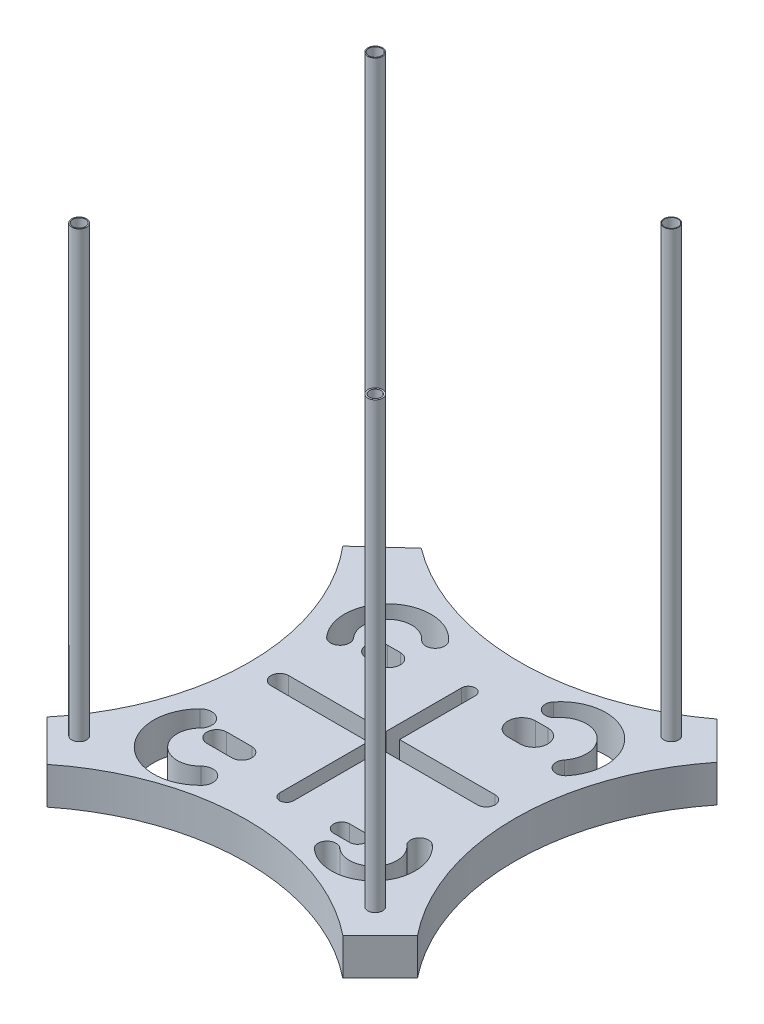
SolidWorks part; units mm, degrees
material "ABS"
ref_plane "Front Plane" through (0, 0, 0) normal (0, 0, 1) x (1, 0, 0)
ref_plane "Top Plane" through (0, 0, 0) normal (0, 1, 0) x (1, 0, 0)
ref_plane "Right Plane" through (0, 0, 0) normal (1, 0, 0) x (0, 0, -1)
sketch "Sketch1" plane through (0, 0, 0) normal (0, 1, 0) x (1, 0, 0)
  line L4 (-35.4489, 52.7329) -> (-27.9489, 60.2329)
  line L5 (12.0511, 60.2329) -> (19.5511, 52.7329)
  line L6 (19.5511, 52.7329) -> (19.6053, 52.733)
  line L7 (19.5511, 12.733) -> (12.0511, 5.2329)
  line L9 (-27.9489, 5.2329) -> (-35.4489, 12.7329)
  arc A4 (19.5511, 52.7329) -> (19.5511, 12.733) centre (42.4677, 32.7329) ccw
  arc A5 (-35.4489, 52.7329) -> (-35.4489, 12.7329) centre (-58.3656, 32.7329) cw
  arc A6 (12.0511, 60.2329) -> (-27.9489, 60.2329) centre (-7.9489, 83.1496) cw
  arc A7 (12.0511, 5.2329) -> (-2.9489, 12.3192) centre (-7.9489, -17.6837) ccw
  arc A8 (-12.9489, 12.3192) -> (-27.9489, 5.2329) centre (-7.9489, -17.6837) ccw
  arc A9 (-12.9489, 12.3192) -> (-2.9489, 12.3192) centre (-7.9489, -11.0454) cw
extrude "Boss-Extrude1" add sketch "Sketch1" along normal blind 5
sketch "Sketch3" plane through (0, 5, 0) normal (0, 1, 0) x (1, 0, 0)
  line L0 (-27.9489, 60.2329) -> (-35.4489, 52.7329)
  line L1 (12.0511, 60.2329) -> (19.5511, 52.7329)
  line L2 (-35.4489, 12.7329) -> (-27.9489, 5.2329)
  line L3 (12.0511, 5.2329) -> (19.5511, 12.733)
  line L4 (-33.4937, 12.7329) -> (-27.9489, 7.1882)
  line L5 (12.0511, 7.1882) -> (17.0997, 12.2368)
  line L8 (-33.4937, 52.7329) -> (-27.9489, 57.7816)
  line L9 (12.0511, 57.7816) -> (17.0997, 52.7329)
  arc A0 (-27.9489, 60.2329) -> (12.0511, 60.2329) centre (-7.9489, 83.1496) ccw
  arc A1 (-27.9489, 5.2329) -> (12.0511, 5.2329) centre (-7.9489, -17.2226) cw
  arc A2 (19.5511, 52.7329) -> (19.5511, 12.733) centre (42.4677, 32.7329) ccw
  arc A3 (-35.4489, 52.7329) -> (-35.4489, 12.7329) centre (-58.3656, 32.7329) cw
  arc A4 (17.0997, 52.7329) -> (17.0997, 12.2368) centre (42.4522, 32.4849) ccw
  arc A5 (12.0511, 7.1882) -> (-27.9489, 7.1882) centre (-7.9489, -17.7834) ccw
  arc A6 (-33.4937, 12.7329) -> (-33.4937, 52.7329) centre (-57.2926, 32.7329) ccw
  arc A8 (-27.9489, 57.7816) -> (12.0511, 57.7816) centre (-7.9489, 84.416) ccw
extrude "Cut-Extrude1" cut sketch "Sketch3" against normal blind 15
sketch "Sketch4" plane through (0, 5, 0) normal (0, 1, 0) x (1, 0, 0)
  line L0 (-18.8679, 42.7074) -> (-17.154, 42.7074) construction
  line L1 (-18.8679, 44.1617) -> (-17.154, 44.1617)
  line L2 (-18.8679, 41.2532) -> (-17.154, 41.2532)
  line L3 (0.0021, 43.4256) -> (1.6386, 43.4256) construction
  line L4 (0.0021, 45.3023) -> (1.6386, 45.3023)
  line L5 (0.0021, 41.5489) -> (1.6386, 41.5489)
  line L6 (1.6386, 19.5988) -> (-0.5162, 19.5988) construction
  line L7 (1.6386, 18.5107) -> (-0.5162, 18.5107)
  line L8 (1.6386, 20.6869) -> (-0.5162, 20.6869)
  line L9 (-19.5838, 21.7963) -> (-16.1947, 21.7963) construction
  line L10 (-19.5838, 23.133) -> (-16.1947, 23.133)
  line L11 (-19.5838, 20.4597) -> (-16.1947, 20.4597)
  line L12 (-7.9489, 44.1617) -> (-7.9489, 19.5988) construction
  line L13 (-7.0162, 44.1617) -> (-7.0162, 19.5988)
  line L14 (-8.8816, 44.1617) -> (-8.8816, 19.5988)
  line L15 (-22.0136, 32.7329) -> (5.8881, 32.7329) construction
  line L16 (-22.0136, 33.9255) -> (5.8881, 33.9255)
  line L17 (-22.0136, 31.5403) -> (5.8881, 31.5403)
  arc A0 (-16.1947, 47.9157) -> (-22.9729, 41.8489) centre (-19.5838, 44.8823) ccw construction
  arc A1 (-15.2355, 48.7742) -> (-23.9321, 40.9903) centre (-19.5838, 44.8823) ccw
  arc A2 (-17.154, 47.0571) -> (-22.0136, 42.7074) centre (-19.5838, 44.8823) ccw
  arc A3 (-17.154, 47.0571) -> (-15.2355, 48.7742) centre (-16.1947, 47.9157) ccw
  arc A4 (-23.9321, 40.9903) -> (-22.0136, 42.7074) centre (-22.9729, 41.8489) ccw
  arc A5 (-16.1947, 16.2857) -> (-22.9729, 22.9118) centre (-19.5838, 19.5988) cw construction
  arc A6 (-24.1139, 24.0273) -> (-15.0536, 15.1702) centre (-19.5838, 19.5988) ccw
  arc A7 (-21.8318, 21.7963) -> (-17.3358, 17.4012) centre (-19.5838, 19.5988) ccw
  arc A8 (-21.8318, 21.7963) -> (-24.1139, 24.0273) centre (-22.9729, 22.9118) ccw
  arc A9 (-15.0536, 15.1702) -> (-17.3358, 17.4012) centre (-16.1947, 16.2857) ccw
  arc A10 (7.5246, 41.8489) -> (0.0021, 47.9157) centre (3.7633, 44.8823) ccw construction
  arc A11 (8.5475, 41.0238) -> (-1.0208, 48.7407) centre (3.7633, 44.8823) ccw
  arc A12 (6.5016, 42.6739) -> (1.0251, 47.0907) centre (3.7633, 44.8823) ccw
  arc A13 (6.5016, 42.6739) -> (8.5475, 41.0238) centre (7.5246, 41.8489) ccw
  arc A14 (-1.0208, 48.7407) -> (1.0251, 47.0907) centre (0.0021, 47.9157) ccw
  arc A15 (6.6995, 22.9118) -> (0.8271, 16.2857) centre (3.7633, 19.5988) cw construction
  arc A16 (0.0157, 15.3701) -> (7.511, 23.8274) centre (3.7633, 19.5988) ccw
  arc A17 (1.6386, 17.2013) -> (5.8881, 21.9962) centre (3.7633, 19.5988) ccw
  arc A18 (1.6386, 17.2013) -> (0.0157, 15.3701) centre (0.8271, 16.2857) ccw
  arc A19 (7.511, 23.8274) -> (5.8881, 21.9962) centre (6.6995, 22.9118) ccw
  arc A20 (-18.8679, 44.1617) -> (-18.8679, 41.2532) centre (-18.8679, 42.7074) ccw
  arc A21 (-17.154, 41.2532) -> (-17.154, 44.1617) centre (-17.154, 42.7074) ccw
  arc A22 (0.0021, 45.3023) -> (0.0021, 41.5489) centre (0.0021, 43.4256) ccw
  arc A23 (1.6386, 41.5489) -> (1.6386, 45.3023) centre (1.6386, 43.4256) ccw
  arc A24 (1.6386, 18.5107) -> (1.6386, 20.6869) centre (1.6386, 19.5988) ccw
  arc A25 (-0.5162, 20.6869) -> (-0.5162, 18.5107) centre (-0.5162, 19.5988) ccw
  arc A26 (-19.5838, 23.133) -> (-19.5838, 20.4597) centre (-19.5838, 21.7963) ccw
  arc A27 (-16.1947, 20.4597) -> (-16.1947, 23.133) centre (-16.1947, 21.7963) ccw
  arc A28 (-7.0162, 44.1617) -> (-8.8816, 44.1617) centre (-7.9489, 44.1617) ccw
  arc A29 (-8.8816, 19.5988) -> (-7.0162, 19.5988) centre (-7.9489, 19.5988) ccw
  arc A30 (-22.0136, 33.9255) -> (-22.0136, 31.5403) centre (-22.0136, 32.7329) ccw
  arc A31 (5.8881, 31.5403) -> (5.8881, 33.9255) centre (5.8881, 32.7329) ccw
  point P3 (-22.6172, 48.2713)
  point P11 (-22.8968, 16.2097)
  point P16 (6.7967, 48.6435)
  point P24 (7.0764, 16.6626)
  point P34 (-18.0109, 42.7074)
  point P39 (0.8204, 43.4256)
  point P46 (0.5612, 19.5988)
  point P53 (-17.8892, 21.7963)
  point P63 (-7.9489, 31.8802)
  point P68 (-8.0628, 32.7329)
  point P76 (0, 0)
extrude "Cut-Extrude4" cut sketch "Sketch4" against normal blind 15 contours L11 A27 L10 A26 | A7 A9 A6 A8 | A2 A4 A1 A3 | A20 L2 A21 L1 | L14 A29 L13 A28 | L16 A31 L17 A30 | A12 A14 A11 A13 | A23 L4 A22 L5 | A19 A17 A18 A16 | A24 L8 A25 L7
sketch "Sketch7" plane through (0, 5, 0) normal (0, 1, 0) x (1, 0, 0)
  circle A0 centre (-29.113, 52.7329) radius 1
  circle A1 centre (10.887, 52.7329) radius 1
  circle A2 centre (10.887, 12.7329) radius 1
  circle A3 centre (-29.113, 12.7329) radius 1
  point P12 (0, 0)
extrude "Boss-Extrude2" add sketch "Sketch7" along normal blind 60 contours A2 | A1 | A0 | A3
sketch "Sketch8" plane through (0, 65, 0) normal (0, 1, 0) x (1, 0, 0)
  circle A0 centre (-29.113, 52.7329) radius 0.8734
extrude "Cut-Extrude5" cut sketch "Sketch8" against normal blind 15
sketch "Sketch9" plane through (0, 65, 0) normal (0, 1, 0) x (1, 0, 0)
  circle A0 centre (10.887, 52.7329) radius 0.919
extrude "Cut-Extrude6" cut sketch "Sketch9" against normal blind 15
sketch "Sketch10" plane through (0, 65, 0) normal (0, 1, 0) x (1, 0, 0)
  circle A0 centre (-29.113, 12.7329) radius 0.8592
extrude "Cut-Extrude7" cut sketch "Sketch10" against normal blind 15
sketch "Sketch11" plane through (0, 65, 0) normal (0, 1, 0) x (1, 0, 0)
  circle A0 centre (10.887, 12.7329) radius 0.7869
extrude "Cut-Extrude8" cut sketch "Sketch11" against normal blind 15
